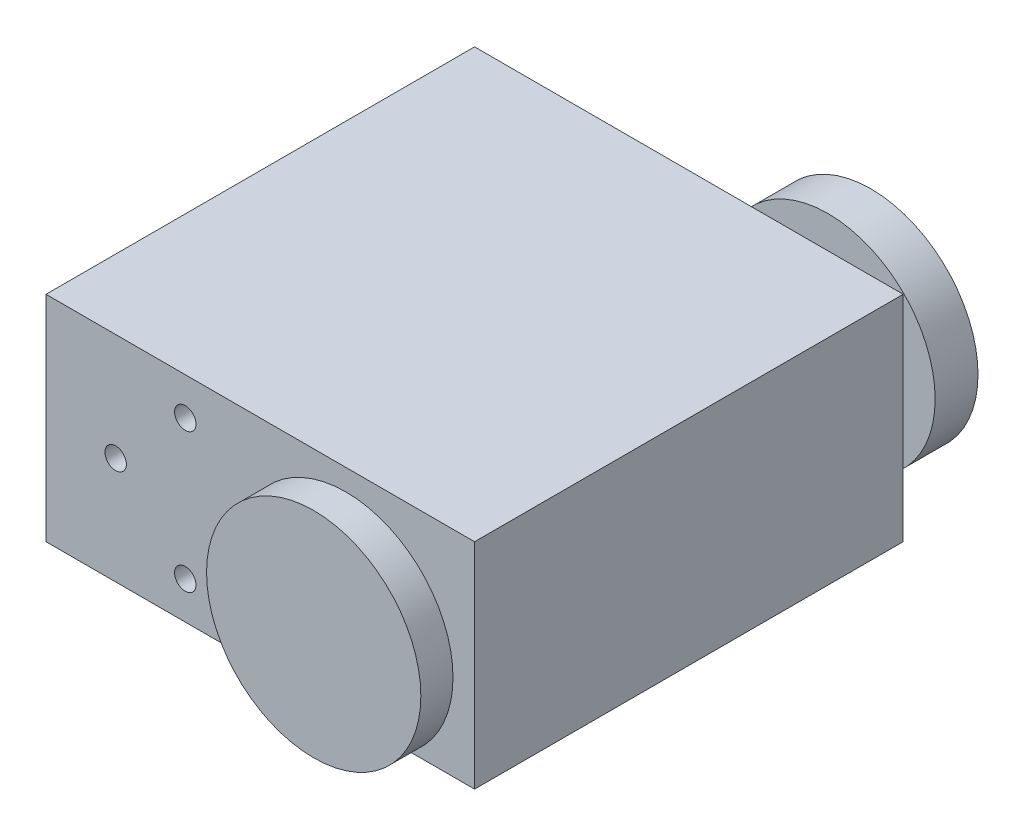
SolidWorks part; units mm, degrees
ref_plane "Front Plane" through (0, 0, 0) normal (0, 0, 1) x (1, 0, 0)
ref_plane "Top Plane" through (0, 0, 0) normal (0, 1, 0) x (1, 0, 0)
ref_plane "Right Plane" through (0, 0, 0) normal (1, 0, 0) x (0, 0, -1)
sketch "Sketch1" plane through (0, 0, 0) normal (0, 1, 0) x (1, 0, 0)
  line L1 (0, 0) -> (40, 0)
  line L2 (0, 0) -> (0, 40)
  line L3 (0, 40) -> (40, 40)
  line L4 (40, 0) -> (40, 40)
  dimension "D1" = 40
  dimension "D2" = 40
extrude "Boss-Extrude1" add sketch "Sketch1" along normal blind 20
sketch "Sketch2" plane through (0, 0, 0) normal (0, 0, 1) x (1, 0, 0)
  circle A0 centre (29.9853, 10.0203) radius 4
  dimension "D1" = 8
extrude "Boss-Extrude2" add sketch "Sketch2" along normal blind 2 and the other way blind 43
sketch "Sketch3" plane through (0, 0, 2) normal (0, 0, 1) x (1, 0, 0)
  circle A0 centre (29.9853, 10.0203) radius 10
  dimension "D1" = 20
extrude "Boss-Extrude3" add sketch "Sketch3" along normal blind 3
sketch "Sketch4" plane through (0, 0, -43) normal (0, 0, -1) x (-1, 0, 0)
  circle A0 centre (-29.9853, 10.0203) radius 10
  dimension "D1" = 20
extrude "Boss-Extrude4" add sketch "Sketch4" along normal blind 4
sketch "Sketch5" plane through (0, 0, -40) normal (0, 0, -1) x (-1, 0, 0)
  circle A0 centre (-5, 18) radius 1
  circle A1 centre (-5, 2) radius 1
  circle A2 centre (-21, 2) radius 1
  circle A3 centre (-21, 18) radius 1
  dimension "D1" = 2
  dimension "D2" = 2
  dimension "D3" = 2
  dimension "D4" = 2
extrude "Cut-Extrude1" cut sketch "Sketch5" against normal blind 5
sketch "Sketch6" plane through (0, 0, 0) normal (0, 0, 1) x (1, 0, 0)
  circle A0 centre (13, 16.5) radius 1
  circle A1 centre (6.5, 10) radius 1
  circle A2 centre (13, 3.5) radius 1
  circle A3 centre (19.5, 10) radius 1
  dimension "D1" = 2
  dimension "D2" = 2
  dimension "D3" = 2
  dimension "D4" = 2
extrude "Cut-Extrude2" cut sketch "Sketch6" against normal blind 5
